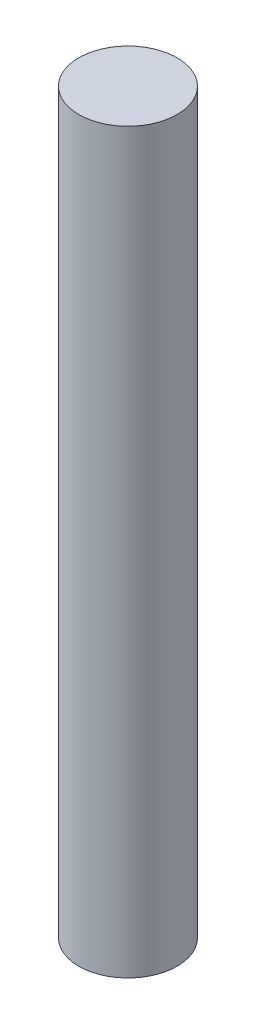
SolidWorks part; units mm, degrees
ref_plane "Front Plane" through (0, 0, 0) normal (0, 0, 1) x (1, 0, 0)
ref_plane "Top Plane" through (0, 0, 0) normal (0, 1, 0) x (1, 0, 0)
ref_plane "Right Plane" through (0, 0, 0) normal (1, 0, 0) x (0, 0, -1)
sketch "Sketch1" plane through (0, 0, 0) normal (0, 1, 0) x (1, 0, 0)
  circle A0 centre (0, 0) radius 4
  dimension "D1" = 8
extrude "Boss-Extrude1" add sketch "Sketch1" along normal mid plane 60
